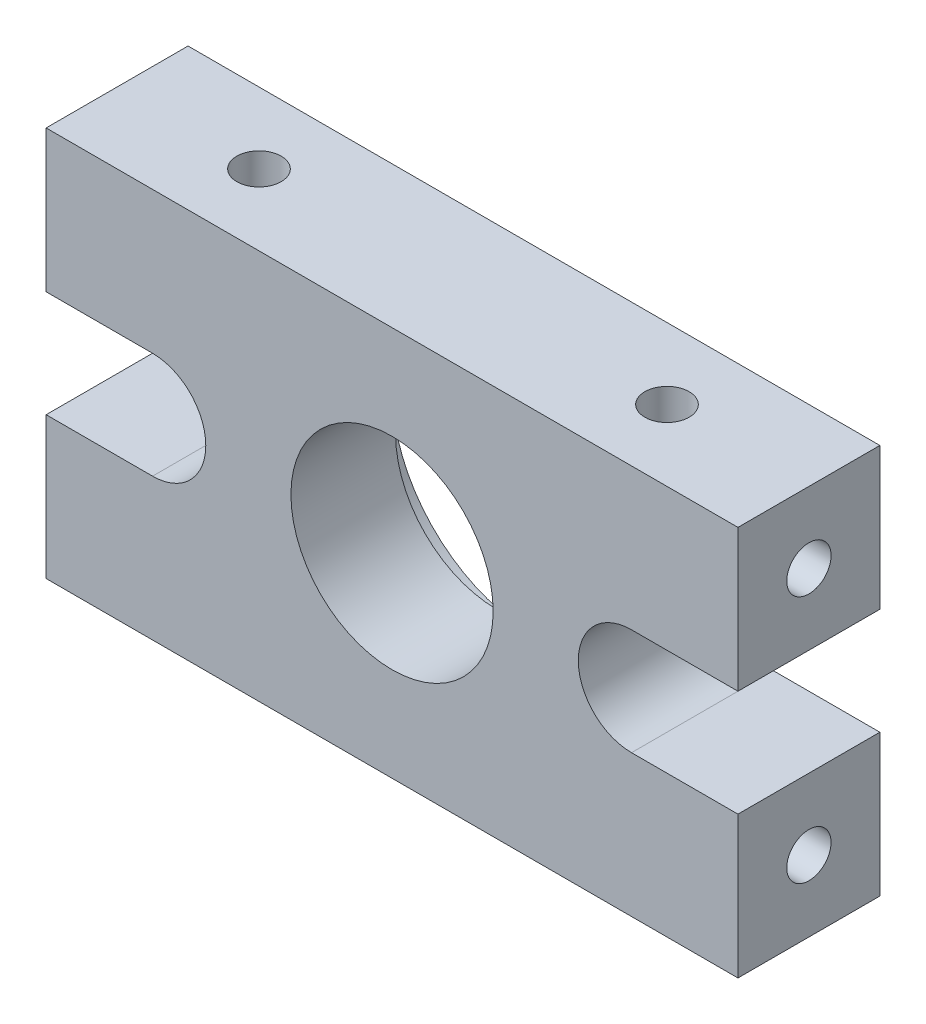
SolidWorks part; units mm, degrees
ref_plane "Front Plane" through (0, 0, 0) normal (0, 0, 1) x (1, 0, 0)
ref_plane "Top Plane" through (0, 0, 0) normal (0, 1, 0) x (1, 0, 0)
ref_plane "Right Plane" through (0, 0, 0) normal (1, 0, 0) x (0, 0, -1)
sketch "Sketch1" plane through (0, 0, 0) normal (0, 0, 1) x (1, 0, 0)
  line L0 (0, 0) -> (39, 0)
  line L1 (39, 0) -> (39, 8)
  line L2 (39, 22) -> (0, 22)
  line L3 (0, 8) -> (0, 0)
  line L4 (0, 8) -> (6, 8)
  line L5 (6, 14) -> (0, 14)
  line L6 (0, 14) -> (0, 22)
  line L7 (39, 8) -> (33, 8)
  line L8 (33, 14) -> (39, 14)
  line L9 (39, 14) -> (39, 22)
  circle A0 centre (19.5, 11) radius 5.7
  arc A1 (6, 8) -> (6, 14) centre (6, 11) ccw
  arc A2 (33, 8) -> (33, 14) centre (33, 11) cw
  dimension "D1" = 11.4
  dimension "D6" = 3
  dimension "D2" = 39
  dimension "D3" = 22
  dimension "D4" = 11
  dimension "D5" = 19.5
  dimension "D7" = 6
extrude "Boss-Extrude1" add sketch "Sketch1" along normal blind 8
hole_wizard "Tap Drill for M3x0.5 Tap1" positions "Sketch3" profile "Sketch2" hole size "M3x0.5" standard "ANSI Metric"
sketch "Sketch3" plane through (39, 0, 0) normal (1, 0, 0) x (0, 0, -1)
  line L0 (-8, 0) -> (-8, 8) construction
  line L1 (-8, 0) -> (0, 0) construction
  line L2 (-8, 22) -> (0, 22) construction
  point P0 (-4, 18)
  point P2 (-4, 4)
  dimension "D1" = 4
  dimension "D2" = 4
  dimension "D3" = 4
sketch "Sketch2" plane through (39, 18, 4) normal (0, 1, 0) x (0, 0, -1)
  line L0 (0, 0) -> (0, 5.7511)
  line L1 (0, 5.7511) -> (1.25, 5)
  line L2 (1.25, 5) -> (1.25, 0)
  line L5 (1.25, 0) -> (0, 0)
  line L10 (0, 5.7511) -> (-1.25, 5) construction
  line L11 (0, -6.35) -> (0, 107.95) construction
  dimension "Hole Dia." = 2.5
  dimension "Hole Depth" = 5
  dimension "Drill Angle" = 118
hole_wizard "Tap Drill for M3x0.5 Tap2" positions "Sketch5" profile "Sketch4" hole size "M3x0.5" standard "ANSI Metric"
sketch "Sketch5" plane through (0, 0, 0) normal (-1, 0, 0) x (0, 0, 1)
  line L0 (8, 22) -> (8, 14) construction
  line L1 (8, 22) -> (0, 22) construction
  line L2 (8, 0) -> (0, 0) construction
  point P0 (4, 4)
  point P2 (4, 18)
  dimension "D1" = 4
  dimension "D2" = 4
  dimension "D3" = 4
sketch "Sketch4" plane through (0, 4, 4) normal (0, 1, 0) x (0, 0, 1)
  line L0 (0, 0) -> (0, 5.7511)
  line L1 (0, 5.7511) -> (1.25, 5)
  line L2 (1.25, 5) -> (1.25, 0)
  line L5 (1.25, 0) -> (0, 0)
  line L10 (0, 5.7511) -> (-1.25, 5) construction
  line L11 (0, -6.35) -> (0, 107.95) construction
  dimension "Hole Dia." = 2.5
  dimension "Hole Depth" = 5
  dimension "Drill Angle" = 118
hole_wizard "Tap Drill for M3x0.5 Tap3" positions "Sketch7" profile "Sketch6" hole size "M3x0.5" standard "ANSI Metric"
sketch "Sketch7" plane through (0, 22, 0) normal (0, 1, 0) x (1, 0, 0)
  line L0 (0, -8) -> (0, 0) construction
  line L1 (39, 0) -> (0, 0) construction
  line L2 (39, -8) -> (39, 0) construction
  point P0 (31, -4)
  point P2 (8, -4)
  dimension "D1" = 8
  dimension "D2" = 4
  dimension "D3" = 8
sketch "Sketch6" plane through (31, 22, 4) normal (1, 0, 0) x (0, 0, 1)
  line L0 (0, 0) -> (0, 5.7511)
  line L1 (0, 5.7511) -> (1.25, 5)
  line L2 (1.25, 5) -> (1.25, 0)
  line L5 (1.25, 0) -> (0, 0)
  line L10 (0, 5.7511) -> (-1.25, 5) construction
  line L11 (0, -6.35) -> (0, 107.95) construction
  dimension "Hole Dia." = 2.5
  dimension "Hole Depth" = 5
  dimension "Drill Angle" = 118
sketch "Sketch8" plane through (0, 0, 0) normal (0, 0, -1) x (-1, 0, 0)
  circle A0 centre (-19.5, 11) radius 8
  dimension "D1" = 16
extrude "Cut-Extrude1" cut sketch "Sketch8" against normal blind 2.1
